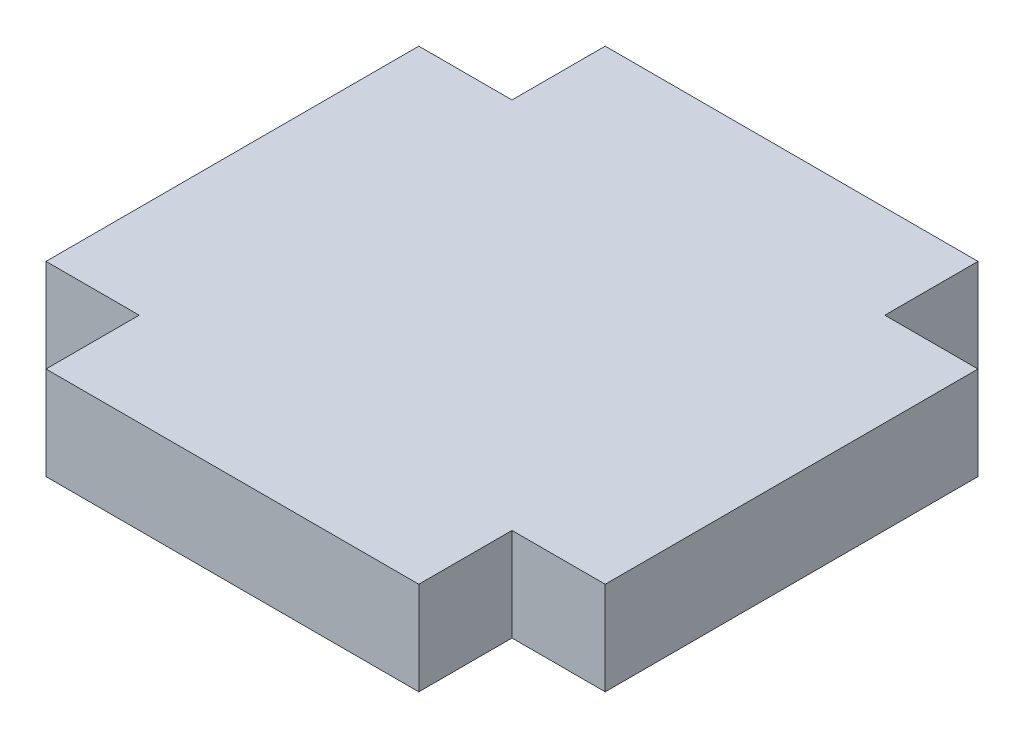
SolidWorks part; units mm, degrees
ref_plane "Front Plane" through (0, 0, 0) normal (0, 0, 1) x (1, 0, 0)
ref_plane "Top Plane" through (0, 0, 0) normal (0, 1, 0) x (1, 0, 0)
ref_plane "Right Plane" through (0, 0, 0) normal (1, 0, 0) x (0, 0, -1)
sketch "Sketch1" plane through (0, 0, 0) normal (0, 1, 0) x (1, 0, 0)
  line L0 (-9.525, 6.35) -> (-9.525, -6.35)
  line L1 (-9.525, -6.35) -> (-6.35, -6.35)
  line L2 (-6.35, -6.35) -> (-6.35, -9.525)
  line L3 (-6.35, -9.525) -> (6.35, -9.525)
  line L4 (6.35, -9.525) -> (6.35, -6.35)
  line L5 (6.35, -6.35) -> (9.525, -6.35)
  line L6 (9.525, -6.35) -> (9.525, 6.35)
  line L7 (9.525, 6.35) -> (6.35, 6.35)
  line L8 (6.35, 6.35) -> (6.35, 9.525)
  line L9 (6.35, 9.525) -> (-6.35, 9.525)
  line L10 (-6.35, 9.525) -> (-6.35, 6.35)
  line L11 (-6.35, 6.35) -> (-9.525, 6.35)
  point P2 (0, 9.525)
  point P13 (9.525, 0)
  dimension "D1" = 3.175
  dimension "D2" = 12.7
extrude "Boss-Extrude1" add sketch "Sketch1" along normal mid plane 3.175
